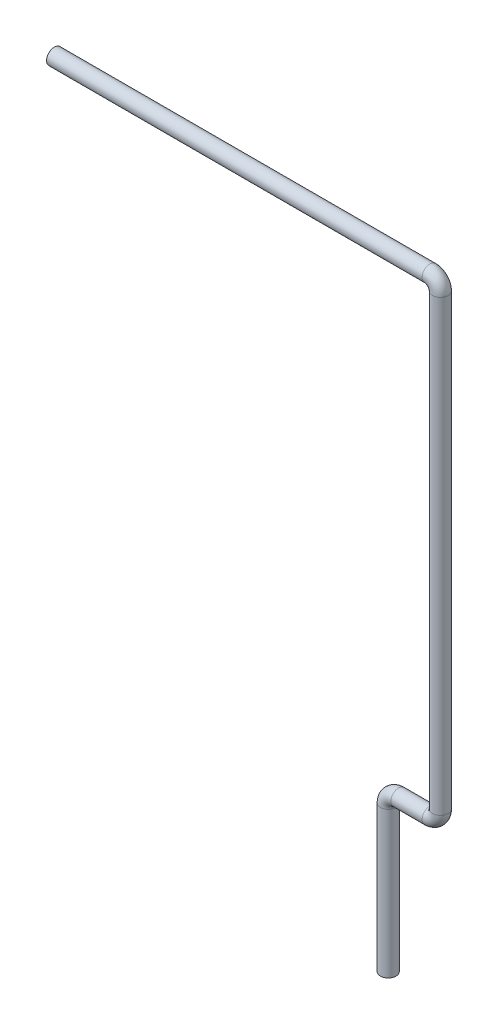
SolidWorks part; units mm, degrees
ref_plane "Front Plane" through (0, 0, 0) normal (0, 0, 1) x (1, 0, 0)
ref_plane "Top Plane" through (0, 0, 0) normal (0, 1, 0) x (1, 0, 0)
ref_plane "Right Plane" through (0, 0, 0) normal (1, 0, 0) x (0, 0, -1)
sketch "Sketch1" plane through (0, 0, 0) normal (0, 0, 1) x (1, 0, 0)
  line L0 (0, 0) -> (360, 0)
  line L1 (370, -10) -> (370, -440)
  line L2 (360, -450) -> (330, -450)
  line L3 (320, -460) -> (320, -600)
  arc A0 (360, 0) -> (370, -10) centre (360, -10) cw
  arc A1 (370, -440) -> (360, -450) centre (360, -440) cw
  arc A2 (330, -450) -> (320, -460) centre (330, -460) ccw
  point P11 (15.3447, -65.1349)
  dimension "D1" = 10
  dimension "D2" = 10
  dimension "D3" = 10
  dimension "D4" = 600
  dimension "D5" = 450
  dimension "D6" = 370
  dimension "D7" = 50
sketch "Sketch2" plane through (0, 0, 0) normal (1, 0, 0) x (0, 0, -1)
  circle A0 centre (0, 0) radius 6
  dimension "D1" = 12
sweep "Sweep-Thin1" add profiles "Sketch2" path "Sketch1" parameters "D1"=1.5
sketch "Sketch3" plane through (0, 0, 0) normal (0, 1, 0) x (1, 0, 0)
  line L0 (-39.2897, 0) -> (409.3809, 0) construction
  circle A0 centre (19.1131, 0) radius 2.5
  circle A1 centre (39.1131, 0) radius 2.5
  circle A2 centre (59.1131, 0) radius 2.5
  circle A3 centre (79.1131, 0) radius 2.5
  circle A4 centre (99.1131, 0) radius 2.5
  circle A5 centre (119.1131, 0) radius 2.5
  circle A6 centre (139.1131, 0) radius 2.5
  circle A7 centre (159.1131, 0) radius 2.5
  circle A8 centre (179.1131, 0) radius 2.5
  circle A9 centre (199.1131, 0) radius 2.5
  circle A10 centre (219.1131, 0) radius 2.5
  circle A11 centre (239.1131, 0) radius 2.5
  circle A12 centre (259.1131, 0) radius 2.5
  circle A13 centre (279.1131, 0) radius 2.5
  circle A14 centre (299.1131, 0) radius 2.5
  circle A15 centre (319.1131, 0) radius 2.5
  circle A16 centre (339.1131, 0) radius 2.5
  dimension "D1" = 5
  dimension "D2" = 17
extrude "Cut-Extrude1" cut sketch "Sketch3" against normal blind 10
surface "Surface-Fill1"
